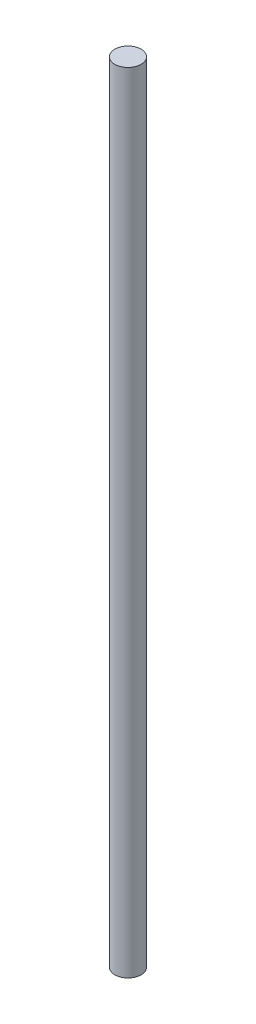
SolidWorks part; units mm, degrees
ref_plane "Alzado" through (0, 0, 0) normal (0, 0, 1) x (1, 0, 0)
ref_plane "Planta" through (0, 0, 0) normal (0, 1, 0) x (1, 0, 0)
ref_plane "Vista lateral" through (0, 0, 0) normal (1, 0, 0) x (0, 0, -1)
sketch "Sketch1" plane through (0, 0, 0) normal (0, 1, 0) x (1, 0, 0)
  circle A0 centre (0, 0) radius 2.5
  dimension "D1" = 5
extrude "Boss-Extrude1" add sketch "Sketch1" along normal blind 150
